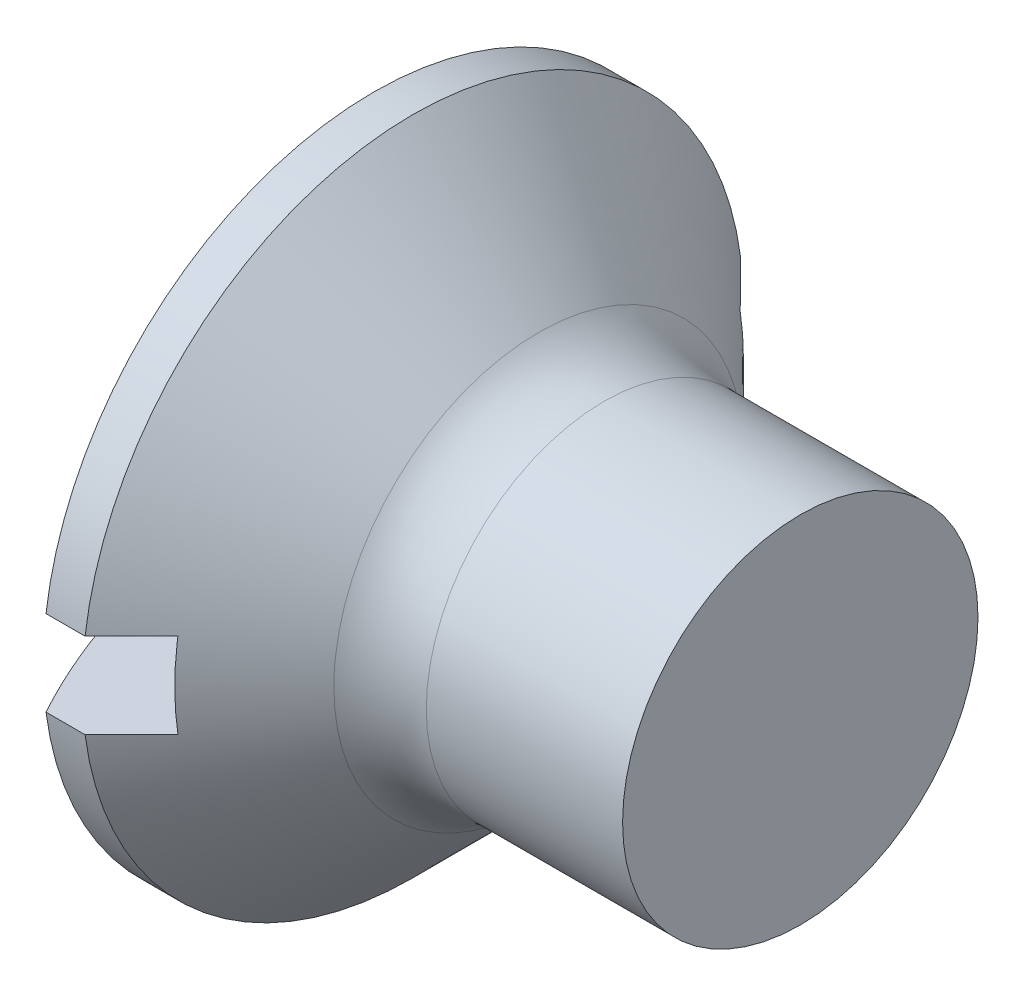
SolidWorks part; units mm, degrees
ref_plane "Plane1" through (0, 0, 0) normal (0, 0, 1) x (1, 0, 0)
ref_plane "Plane2" through (0, 0, 0) normal (0, 1, 0) x (1, 0, 0)
ref_plane "Plane3" through (0, 0, 0) normal (1, 0, 0) x (0, 0, -1)
sketch "BodySke" plane through (0, 0, 0) normal (0, 0, 1) x (1, 0, 0)
  line L0 (0, 0) -> (7.2, 0)
  line L1 (7.2, 0) -> (7.2, 2.5)
  line L2 (7.2, 2.5) -> (3.9, 2.5)
  line L3 (1.75, -4.65) -> (3.9, -2.5) construction
  line L4 (-15.875, 0) -> (82.55, 0) construction
  line L5 (1.75, 4.65) -> (3.9, 2.5)
  line L6 (4.7, 5.675) -> (4.7, -10.2) construction
  line L7 (-0.8, 2.7793) -> (-0.8, -13.0957) construction
  line L8 (1.75, 4.65) -> (1.2, 4.65)
  arc A0 (0, 0) -> (1.2, 4.65) centre (9.6094, 0) cw
  dimension "Length" = 6
  dimension "Diameter" = 5
  dimension "Head_dia" = 9.3
  dimension "Head_ang" = 90
  dimension "Advance" = 0.8
  dimension "Thread_nom" = 8
  dimension "Oval_ht" = 1.2
  dimension "Side_ht" = 2.7
revolve "Base-Revolve" add sketch "BodySke"
cosmetic thread "ThreadCosmetic"
extrude "Slot" cut sketch "Sketch2" along normal blind 2.4
sketch "Sketch2" plane through (0, 0, 0) normal (1, 0, 0) x (0, 0, -1)
  line L0 (4.65, -0.6) -> (-4.65, -0.6)
  line L1 (4.65, -0.6) -> (4.65, 0.6)
  line L2 (-4.65, 0.6) -> (4.65, 0.6)
  line L3 (-4.65, 0.6) -> (-4.65, -0.6)
  dimension "D1" = 9.3
  dimension "Slot_width" = 1.2
  dimension "D3" = 4.65
  dimension "D4" = 0.6
fillet "Fillet1" radius 1.3 1 edges at (3.9, 0, 2.5)
sketch "ThdSchSke" plane through (0, 0, 0) normal (0, 0, 1) x (1, 0, 0)
  line L0 (4.7, -2.055) -> (4.3884, -2.5)
  line L1 (4.7, -2.055) -> (5.0116, -2.5)
  line L2 (5.0116, -2.5) -> (5.0116, -3.125)
  line L3 (-3.175, 0) -> (5.1513, 0) construction
  line L5 (5.0116, -3.125) -> (4.3884, -3.125)
  line L6 (4.3884, -3.125) -> (4.3884, -2.5)
  dimension "Thread_minor" = 4.11
  dimension "Diameter" = 5
  dimension "Start" = 4.7
  dimension "SideAngle" = 55
  dimension "VeeAngle" = 70
  dimension "Overcut" = 6.25
revolve "ThreadSchematic" [suppressed] cut sketch "ThdSchSke" angle 360 about L3
pattern_linear "ThdSchPat" [suppressed]
equation "\"D1@Sketch2\" = \"Head_dia@BodySke\""
equation "\"D3@Sketch2\" = \"D1@Sketch2\" / 2"
equation "\"D4@Sketch2\" = \"Slot_width@Sketch2\" / 2"
equation "\"Thread_length@ThreadCosmetic\" = ((sgn( (\"Length@BodySke\" - \"Advance@BodySke\" - \"Side_ht@BodySke\" ) - \"Thread_nom@BodySke\" )-1)*( (\"Length@BodySke\" - \"Advance@BodySke\" - \"Side_ht@BodySke\" ) - \"Thread_nom@BodySke\" ))/-2+ \"Thread_nom@BodySke\""
equation "\"Thread_minor@ThdSchSke\" = \"Thread_minor@ThreadCosmetic\""
equation "\"Diameter@ThdSchSke\" = \"Diameter@BodySke\""
equation "\"Overcut@ThdSchSke\" = \"Diameter@BodySke\" * 1.25"
equation "\"Start@ThdSchSke\" = \"Oval_ht@BodySke\" + \"Length@BodySke\" - \"Thread_length@ThreadCosmetic\"  '---Countersunk---"
equation "\"Num_threads@ThdSchPat\" = int( \"Thread_length@ThreadCosmetic\" / \"Advance@BodySke\" + 0.999 )  + 1"
equation "\"Advance@ThdSchPat\" = \"Thread_length@ThreadCosmetic\" /  (\"Num_threads@ThdSchPat\" - 1) 'relax it"
